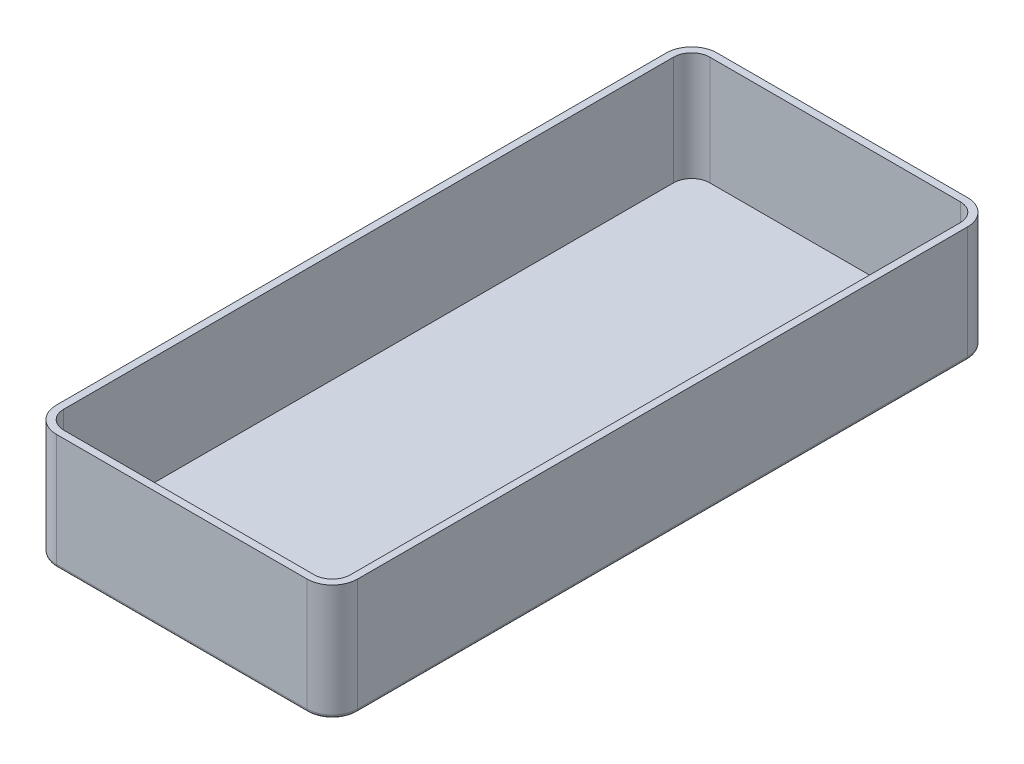
SolidWorks part; units mm, degrees
material "PP Кополимер"
ref_plane "Спереди" through (0, 0, 0) normal (0, 0, 1) x (1, 0, 0)
ref_plane "Сверху" through (0, 0, 0) normal (0, 1, 0) x (1, 0, 0)
ref_plane "Справа" through (0, 0, 0) normal (1, 0, 0) x (0, 0, -1)
sketch "Эскиз1" plane through (0, 0, 0) normal (0, 1, 0) x (1, 0, 0)
  line L1 (-7, 0) -> (-76, 0)
  line L2 (0, 7) -> (0, 175)
  line L3 (-7, 182) -> (-76, 182)
  line L4 (-83, 7) -> (-83, 175)
  arc A0 (-76, 0) -> (-83, 7) centre (-76, 7) cw
  arc A1 (-7, 0) -> (0, 7) centre (-7, 7) ccw
  arc A2 (0, 175) -> (-7, 182) centre (-7, 175) ccw
  arc A3 (-76, 182) -> (-83, 175) centre (-76, 175) ccw
  point P7 (-83, 0)
  point P10 (0, 0)
  point P13 (0, 182)
  dimension "D3" = 7
  dimension "D1" = 182
  dimension "D2" = 83
extrude "Бобышка-Вытянуть1" add sketch "Эскиз1" along normal blind 32
fillet "Скругление1" radius 1 8 edges at (-80.9497, 0, -2.0503) (-83, 0, -91) (-80.9497, 0, -179.9497) (-41.5, 0, -182) (-2.0503, 0, -179.9497) (0, 0, -91) (-2.0503, 0, -2.0503) (-41.5, 0, 0)
shell "Оболочка2" thickness 2
